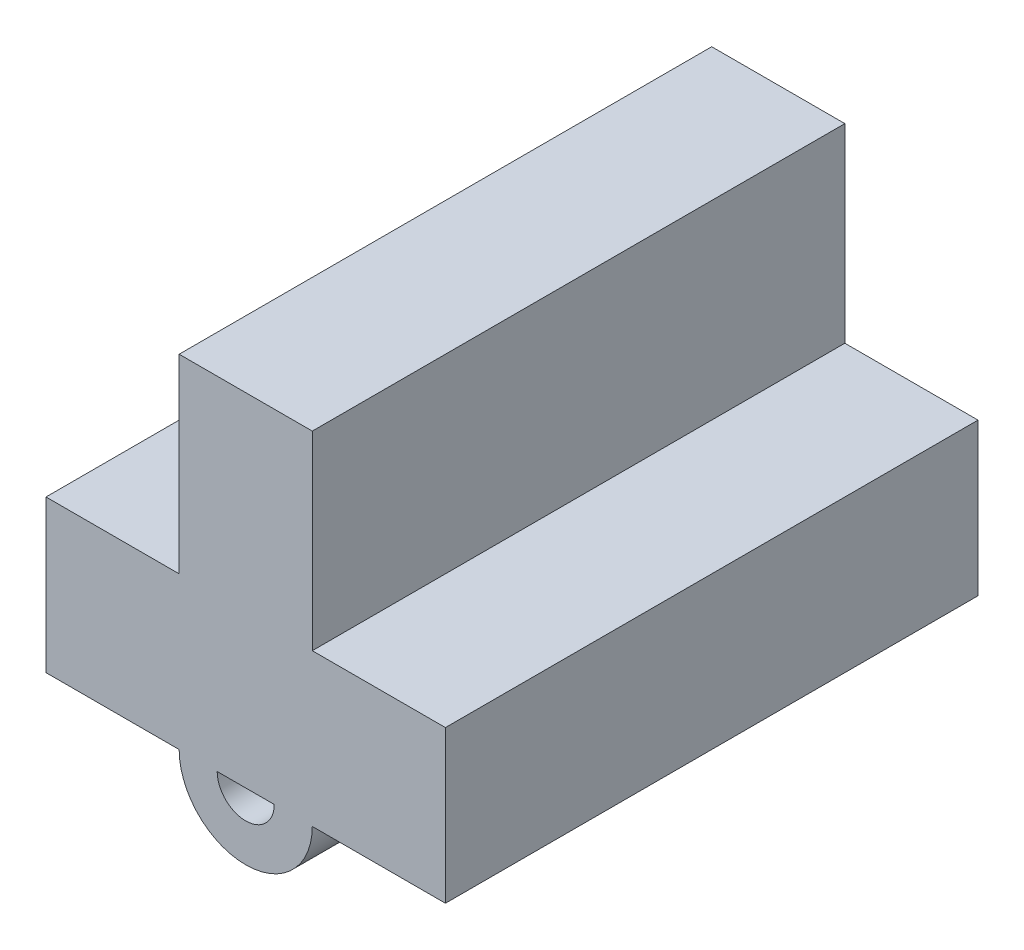
SolidWorks part; units mm, degrees
ref_plane "Front Plane" through (0, 0, 0) normal (0, 0, 1) x (1, 0, 0)
ref_plane "Top Plane" through (0, 0, 0) normal (0, 1, 0) x (1, 0, 0)
ref_plane "Right Plane" through (0, 0, 0) normal (1, 0, 0) x (0, 0, -1)
sketch "Sketch1" plane through (0, 0, 0) normal (0, 0, 1) x (1, 0, 0)
  line L0 (1.75, 2) -> (1.75, 7)
  line L1 (-5.25, -2) -> (5.25, -2)
  line L2 (-5.25, -2) -> (-5.25, 2)
  line L3 (-5.25, 2) -> (-1.75, 2)
  line L4 (5.25, -2) -> (5.25, 2)
  line L5 (-5.25, -2) -> (5.25, 2) construction
  line L6 (-5.25, 2) -> (5.25, -2) construction
  line L7 (1.75, 7) -> (-1.75, 7)
  line L8 (-1.75, 7) -> (-1.75, 2)
  line L9 (1.75, 2) -> (5.25, 2)
  point P0 (0, 0)
  point P8 (0, 7)
  point P11 (0, -2)
  dimension "D1" = 10.5
  dimension "D2" = 4
  dimension "D3" = 5
  dimension "D4" = 3.5
extrude "Boss-Extrude1" add sketch "Sketch1" along normal blind 14
sketch "Sketch2" plane through (0, 0, 14) normal (0, 0, 1) x (1, 0, 0)
  line L0 (-5.25, -2) -> (5.25, -2) construction
  line L1 (-1.75, -2) -> (-0.75, -2)
  line L2 (0.75, -2) -> (1.75, -2)
  arc A0 (-1.75, -2) -> (1.75, -2) centre (0, -2) ccw
  arc A1 (-0.75, -2) -> (0.75, -2) centre (0, -2) ccw
extrude "Boss-Extrude2" add sketch "Sketch2" against normal blind 5
